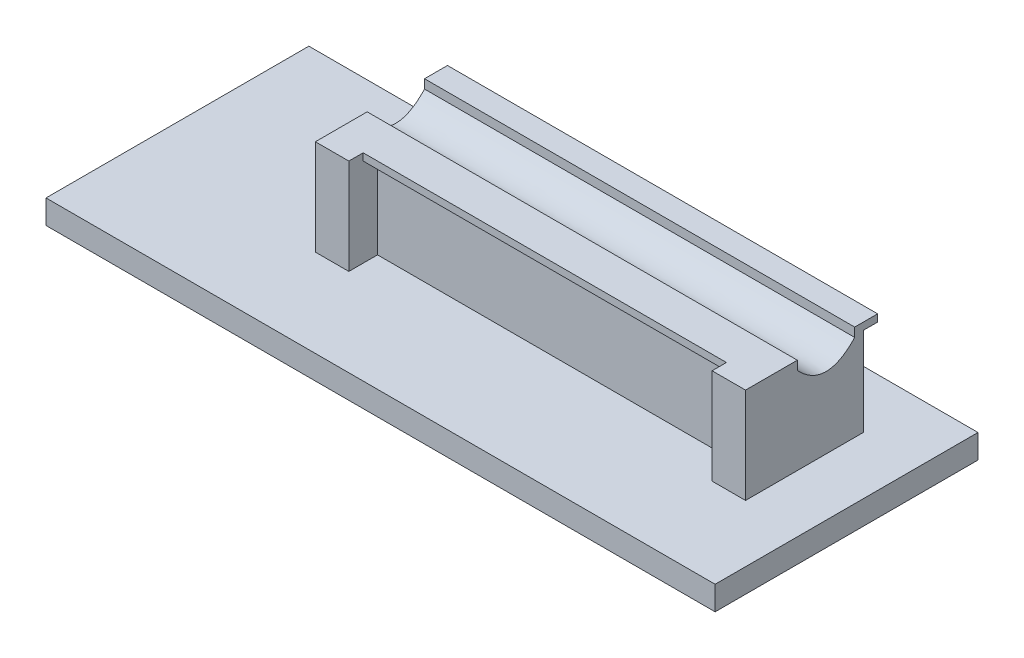
SolidWorks part; units mm, degrees
material "Default (3)"
ref_plane "Front Plane" through (0, 0, 0) normal (0, 0, 1) x (1, 0, 0)
ref_plane "Top Plane" through (0, 0, 0) normal (0, 1, 0) x (1, 0, 0)
ref_plane "Right Plane" through (0, 0, 0) normal (1, 0, 0) x (0, 0, -1)
sketch "Sketch2" plane through (0, 0, 0) normal (1, 0, 0) x (0, 0, -1)
  line L1 (-93.185, 100) -> (93.185, 100)
  line L2 (-93.185, 100) -> (-93.185, -100)
  line L3 (-93.185, -100) -> (93.185, -100)
  line L4 (93.185, 100) -> (93.185, -100)
  line L5 (-93.185, 100) -> (93.185, -100) construction
  line L6 (-93.185, -100) -> (93.185, 100) construction
  point P0 (0, 0)
  dimension "D1" = 200
  dimension "D2" = 186.37
extrude "Boss-Extrude2" add sketch "Sketch2" against normal blind 900
sketch "Sketch3" plane through (0, 0, 93.185) normal (0, 0, 1) x (1, 0, 0)
  line L0 (-900, 100) -> (0, 100) construction
  line L1 (-70, 100) -> (0, 100)
  line L2 (-70, 100) -> (-70, -100)
  line L3 (-70, -100) -> (0, -100)
  line L4 (0, 100) -> (0, -100)
  line L5 (-900, -100) -> (0, -100) construction
  line L6 (-900, 100) -> (-830, 100)
  line L7 (-900, 100) -> (-900, -100)
  line L8 (-900, -100) -> (-830, -100)
  line L9 (-830, 100) -> (-830, -100)
  dimension "D1" = 70
  dimension "D2" = 70
extrude "Boss-Extrude3" add sketch "Sketch3" along normal blind 60
sketch "Sketch4" plane through (0, -100, 0) normal (0, -1, 0) x (1, 0, 0)
  line L0 (-1280, -213.185) -> (-1280, 336.815)
  line L5 (-1280, 336.815) -> (120, 336.815)
  line L6 (120, 336.815) -> (120, -213.185)
  line L7 (120, -213.185) -> (-1280, -213.185)
  line L10 (-900, -93.185) -> (0, -93.185) construction
  line L11 (0, 153.185) -> (0, -93.185) construction
  dimension "D1" = 120
  dimension "D2" = 120
  dimension "D3" = 1400
  dimension "D4" = 550
extrude "Boss-Extrude4" add sketch "Sketch4" along normal blind 50
sketch "Sketch6" plane through (0, 0, 0) normal (1, 0, 0) x (0, 0, -1)
  line L0 (75.185, 123.6488) -> (75.185, 17.6515) construction
  line L2 (93.185, -100) -> (93.185, 100) construction
  line L6 (-44.815, 123.6488) -> (-44.815, 17.6515) construction
  line L7 (-44.815, 100) -> (-44.815, 81.2421)
  line L8 (93.185, 100) -> (-153.185, 100) construction
  line L9 (75.185, 100) -> (75.185, 81.2421)
  line L10 (15.185, 114.2917) -> (15.185, 78.0063) construction
  line L11 (-44.815, 100) -> (75.185, 100)
  spline S0 degree 2 poles (-44.815, 81.2421) (15.185, 17.3999) (75.185, 81.2421) knots 0 0 0 1 1 1
  dimension "D1" = 18
  dimension "D2" = 120
  dimension "D3" = 60
extrude "Cut-Extrude1" cut sketch "Sketch6" against normal blind 900
sketch "Sketch7" plane through (0, 0, -93.185) normal (0, 0, -1) x (-1, 0, 0)
  line L0 (900, -100) -> (900, 100) construction
  line L1 (0, 100) -> (900, 100)
  line L2 (0, 100) -> (0, 85)
  line L3 (0, 85) -> (900, 85)
  line L4 (900, 100) -> (900, 85)
  dimension "D1" = 15
extrude "Boss-Extrude5" add sketch "Sketch7" along normal blind 30
sketch "Sketch8" plane through (0, 0, 93.185) normal (0, 0, 1) x (1, 0, 0)
  line L0 (-70, 100) -> (-70, -100) construction
  line L1 (-830, 100) -> (-70, 100)
  line L2 (-830, 100) -> (-830, 85)
  line L3 (-830, 85) -> (-70, 85)
  line L4 (-70, 100) -> (-70, 85)
  dimension "D1" = 15
extrude "Boss-Extrude6" add sketch "Sketch8" along normal blind 30
